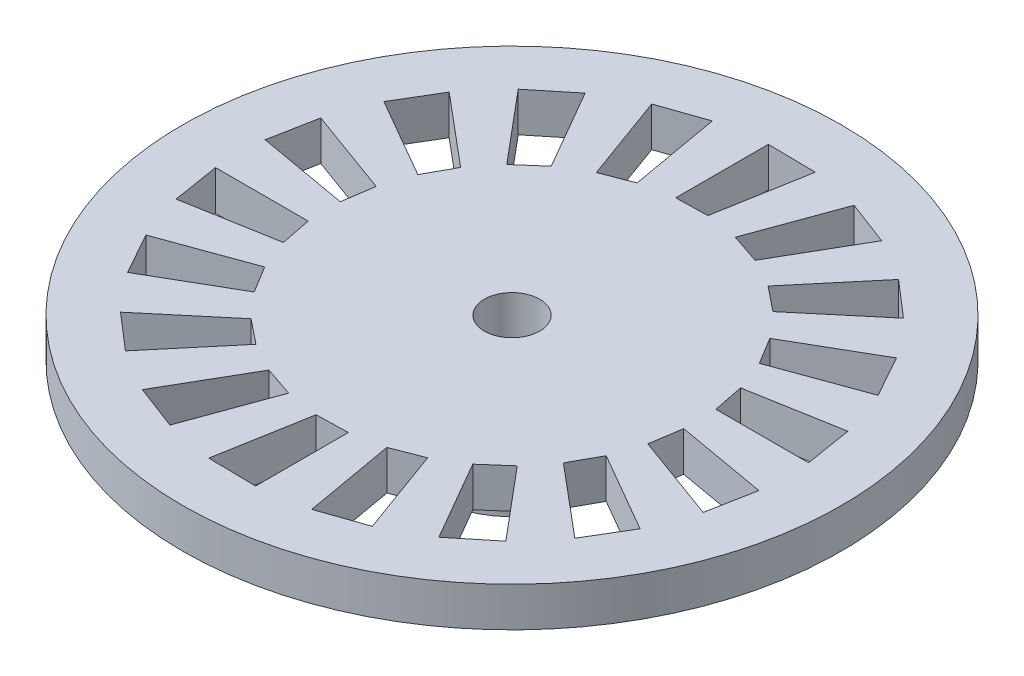
SolidWorks part; units mm, degrees
ref_plane "Front Plane" through (0, 0, 0) normal (0, 0, 1) x (1, 0, 0)
ref_plane "Top Plane" through (0, 0, 0) normal (0, 1, 0) x (1, 0, 0)
ref_plane "Right Plane" through (0, 0, 0) normal (1, 0, 0) x (0, 0, -1)
sketch "스케치1" plane through (0, 0, 0) normal (0, 1, 0) x (1, 0, 0)
  circle A0 centre (0, 0) radius 12.5
extrude "보스-돌출1" add sketch "스케치1" along normal blind 1.5
sketch "스케치2" plane through (0, 1.5, 0) normal (0, 1, 0) x (1, 0, 0)
  line L0 (0, 0) -> (0, 50000) construction
  line L1 (0, 0) -> (50000, 0) construction
  line L2 (-0.75, 2.803) -> (-0.75, 50002.803) construction
  line L3 (1.2949, 11.8069) -> (8683.7038, 49252.1946) construction
  line L4 (0.0775, 0.4397) -> (8682.4864, 49240.8273) construction
  line L5 (-0.75, 6.9597) -> (0.4448, 6.9859)
  line L6 (0.4448, 6.9859) -> (1.0551, 10.4469)
  line L7 (1.0551, 10.4469) -> (-0.75, 10.4732)
  line L8 (-0.75, 10.4732) -> (-0.75, 6.9597)
  circle A0 centre (0, 0) radius 7 construction
  circle A1 centre (0, 0) radius 10.5 construction
  dimension "D3" = 14
  dimension "D4" = 21
  dimension "D1" = 0.75
  dimension "D2" = 10
  dimension "D5" = 0.775
extrude "컷-돌출1" cut sketch "스케치2" against normal blind 2
sketch "스케치3" plane through (0, 1.5, 0) normal (0, 1, 0) x (1, 0, 0)
  circle A0 centre (0, 0) radius 1.05
  dimension "D1" = 2.1
extrude "컷-돌출2" cut sketch "스케치3" against normal blind 22
sketch "스케치4" plane through (0, 1.5, 0) normal (0, 1, 0) x (1, 0, 0)
  circle A0 centre (0, 0) radius 3
  dimension "D1" = 6
extrude "보스-돌출2" add sketch "스케치4" against normal blind 3 from surface at -1.5 starting at face at (0, 0, 1.05)
pattern_circular "원형 패턴1" count 18 every 20 about axis through (0, 0, 0) along (0, 1, 0) of "컷-돌출1"
sketch "스케치5" plane through (0, 1.5, 0) normal (0, 1, 0) x (1, 0, 0)
  circle A0 centre (0, 0) radius 1.05
  dimension "D1" = 2.1
extrude "컷-돌출3" cut sketch "스케치5" against normal blind 23
